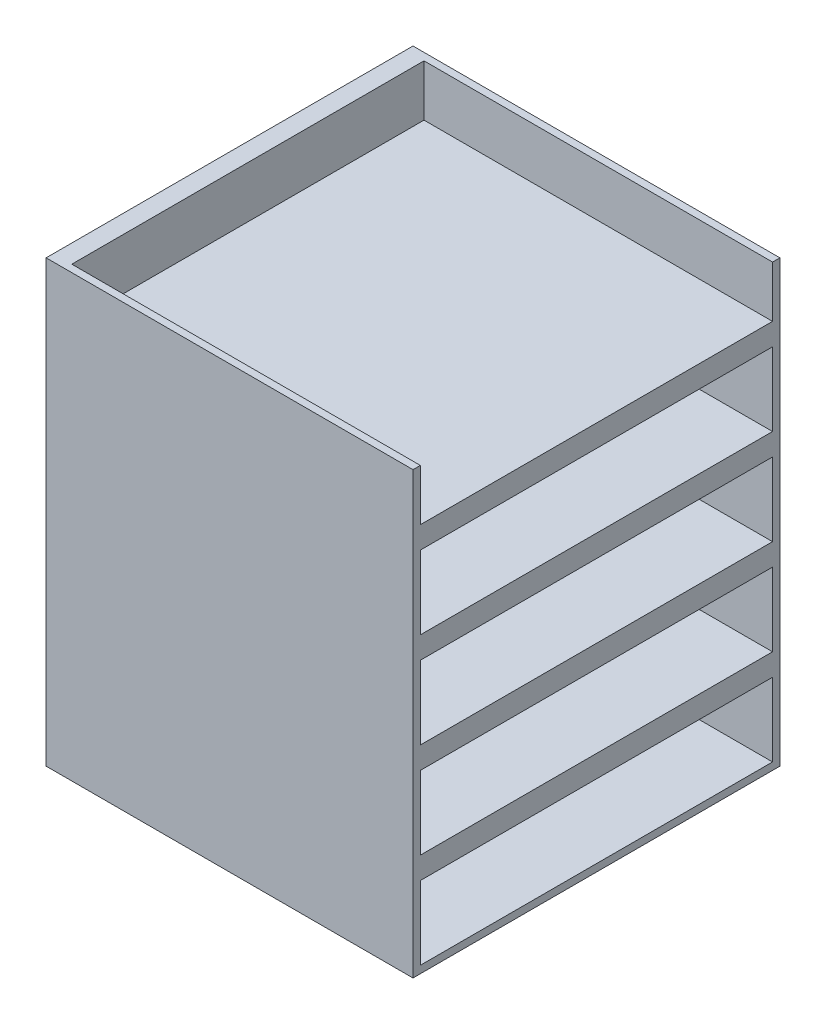
SolidWorks part; units mm, degrees
ref_plane "Front Plane" through (0, 0, 0) normal (0, 0, 1) x (1, 0, 0)
ref_plane "Top Plane" through (0, 0, 0) normal (0, 1, 0) x (1, 0, 0)
ref_plane "Right Plane" through (0, 0, 0) normal (1, 0, 0) x (0, 0, -1)
sketch "Sketch1" plane through (0, 0, 0) normal (0, 1, 0) x (1, 0, 0)
  line L1 (-250, 250) -> (250, 250)
  line L2 (-250, 250) -> (-250, -250)
  line L3 (-250, -250) -> (250, -250)
  line L4 (250, 250) -> (250, -250)
  line L5 (-250, 250) -> (250, -250) construction
  line L6 (-250, -250) -> (250, 250) construction
  point P0 (0, 0)
  dimension "D1" = 500
  dimension "D2" = 500
extrude "Boss-Extrude1" add sketch "Sketch1" along normal blind 600
sketch "Sketch3" plane through (250, 0, 0) normal (1, 0, 0) x (0, 0, -1)
  line L0 (0, 600) -> (0, 0) construction
  line L1 (-250, 600) -> (250, 600) construction
  line L2 (-250, 0) -> (250, 0) construction
  line L3 (240, 110) -> (-240, 110)
  line L4 (240, 110) -> (240, 10)
  line L5 (240, 10) -> (-240, 10)
  line L6 (-240, 110) -> (-240, 10)
  line L7 (240, 110) -> (-240, 10) construction
  line L8 (240, 10) -> (-240, 110) construction
  line L9 (250, 600) -> (250, 0) construction
  line L10 (240, 240) -> (-240, 240)
  line L11 (240, 140) -> (-240, 140)
  line L12 (-240, 240) -> (-240, 140)
  line L13 (240, 240) -> (240, 140)
  line L14 (240, 370) -> (-240, 370)
  line L15 (240, 270) -> (-240, 270)
  line L16 (-240, 370) -> (-240, 270)
  line L17 (240, 370) -> (240, 270)
  line L18 (240, 500) -> (-240, 500)
  line L19 (240, 400) -> (-240, 400)
  line L20 (-240, 500) -> (-240, 400)
  line L21 (240, 500) -> (240, 400)
  line L22 (240, 630) -> (-240, 630)
  line L23 (240, 530) -> (-240, 530)
  line L24 (-240, 630) -> (-240, 530)
  line L25 (240, 630) -> (240, 530)
  point P5 (0, 60)
  dimension "D1" = 10
  dimension "D2" = 10
  dimension "D3" = 100
  dimension "D4" = 5
extrude "Cut-Extrude2" cut sketch "Sketch3" along direction (1, 0, 0) on the side against the normal blind 475
